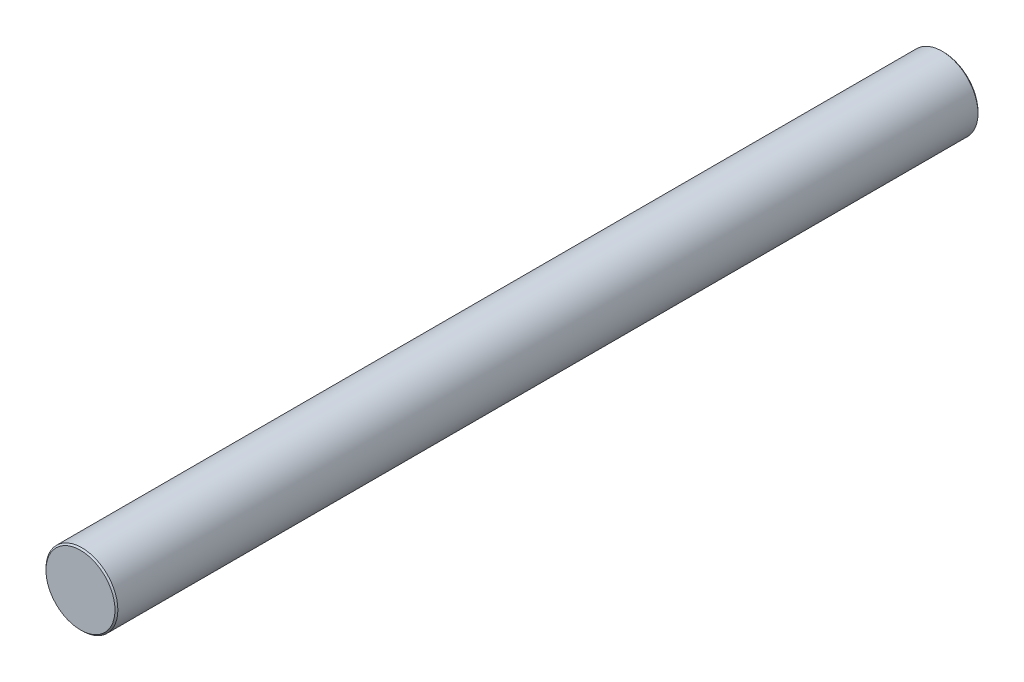
SolidWorks part; units mm, degrees
ref_plane "Front Plane" through (0, 0, 0) normal (0, 0, 1) x (1, 0, 0)
ref_plane "Top Plane" through (0, 0, 0) normal (0, 1, 0) x (1, 0, 0)
ref_plane "Right Plane" through (0, 0, 0) normal (1, 0, 0) x (0, 0, -1)
sketch "Sketch1" plane through (0, 0, 0) normal (0, 0, 1) x (1, 0, 0)
  circle A0 centre (0, 0) radius 12.7 construction
  dimension "Diameter" = 25.4
sketch "Sketch2" plane through (0, 0, 0) normal (1, 0, 0) x (0, 0, -1)
  line L0 (152.4, 0) -> (-152.4, 0) construction
  point P0 (-121.92, 0)
  point P3 (0, 0)
  point P4 (121.92, 0)
  point P6 (-106.68, 0)
  point P7 (106.68, 0)
  dimension "Length" = 304.8
  dimension "D1" = 30.48
  dimension "D2" = 30.48
  dimension "D3" = 45.72
  dimension "D4" = 45.72
sketch "Sketch3" plane through (0, 0, 0) normal (0, 0, 1) x (1, 0, 0)
  circle A0 centre (0, 0) radius 12.7 construction
  circle A1 centre (0, 0) radius 12.7
extrude "Boss-Extrude1" add sketch "Sketch3" along normal up to vertex (152.4 mm away) and the other way up to vertex (152.4 mm away) up to point (0, 0, 152.4) other way up to point (0, 0, -152.4)
chamfer "Chamfer1" distance 0.508 angle 45 2 edges at (12.7, 0, 152.4) (12.7, 0, -152.4)
equation "\"D1@Chamfer1\"=\"Diameter@Sketch1\"*.02"
equation "\"D1@Sketch2\"=\"D2@Sketch2\""
equation "\"D2@Sketch2\"=\"Length@Sketch2\"*.1"
equation "\"D3@Sketch2\"=\"Length@Sketch2\"*.15"
equation "\"D4@Sketch2\"=\"D3@Sketch2\""
